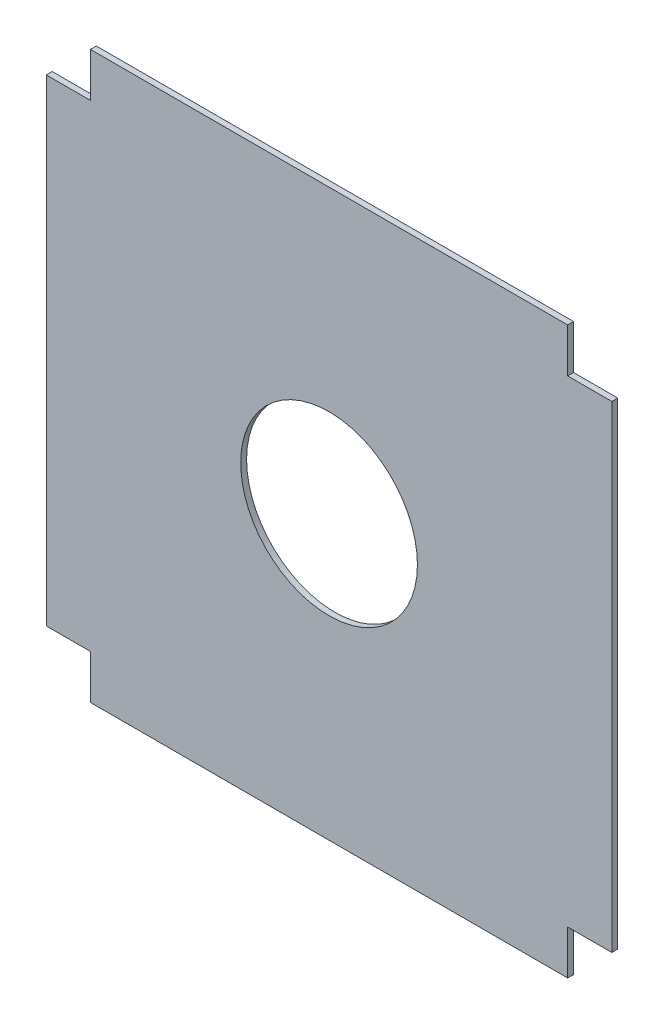
SolidWorks part; units mm, degrees
ref_plane "Front Plane" through (0, 0, 0) normal (0, 0, 1) x (1, 0, 0)
ref_plane "Top Plane" through (0, 0, 0) normal (0, 1, 0) x (1, 0, 0)
ref_plane "Right Plane" through (0, 0, 0) normal (1, 0, 0) x (0, 0, -1)
sketch "Sketch1" plane through (0, 0, 0) normal (0, 0, 1) x (1, 0, 0)
  line L0 (-48, 40.5) -> (-40.5, 40.5)
  line L1 (-40.5, 40.5) -> (-40.5, 48)
  line L2 (-40.5, 48) -> (40.5, 48)
  line L3 (40.5, 48) -> (40.5, 40.5)
  line L4 (40.5, 40.5) -> (48, 40.5)
  line L5 (48, 40.5) -> (48, -40.5)
  line L6 (48, -40.5) -> (40.5, -40.5)
  line L7 (40.5, -40.5) -> (40.5, -48)
  line L8 (40.5, -48) -> (-40.5, -48)
  line L9 (-40.5, -48) -> (-40.5, -40.5)
  line L10 (-40.5, -40.5) -> (-48, -40.5)
  line L11 (-48, -40.5) -> (-48, 40.5)
  point P0 (-40.5, 40.5)
  point P1 (-48, 40.5)
  point P2 (-40.5, 48)
  point P3 (40.5, 48)
  point P4 (40.5, 40.5)
  point P5 (48, 40.5)
  point P6 (-48, -40.5)
  point P7 (-40.5, -40.5)
  point P8 (-40.5, -48)
  point P9 (40.5, -48)
  point P10 (40.5, -40.5)
  point P11 (48, -40.5)
extrude "Boss-Extrude1" add sketch "Sketch1" along normal blind 1
sketch "Sketch2" plane through (0, 0, 1) normal (0, 0, 1) x (1, 0, 0)
  circle A0 centre (0, 0) radius 15
extrude "Cut-Extrude1" cut sketch "Sketch2" against normal blind 10
sketch "Sketch3" plane through (0, 0, 1) normal (0, 0, 1) x (1, 0, 0)
  line L0 (-13, 44) -> (-7, 44)
  line L1 (19, 44) -> (25, 44)
  line L2 (-44, 13) -> (-44, 7)
  line L3 (-44, -19) -> (-44, -25)
  line L4 (-25, -44) -> (-19, -44)
  line L5 (7, -44) -> (13, -44)
  line L6 (44, 25) -> (44, 19)
  line L7 (44, -7) -> (44, -13)
  arc A0 (25, 44) -> (-13, 44) centre (6, 44) cw
  arc A1 (19, 44) -> (-7, 44) centre (6, 44) cw
  arc A2 (-44, 13) -> (-44, -25) centre (-44, -6) cw
  arc A3 (-44, 7) -> (-44, -19) centre (-44, -6) cw
  arc A4 (-25, -44) -> (13, -44) centre (-6, -44) cw
  arc A5 (-19, -44) -> (7, -44) centre (-6, -44) cw
  arc A6 (44, -13) -> (44, 25) centre (44, 6) cw
  arc A7 (44, -7) -> (44, 19) centre (44, 6) cw
  point P2 (-13, 44)
  point P4 (-7, 44)
  point P5 (19, 44)
  point P6 (25, 44)
  point P11 (-44, 13)
  point P12 (-44, 7)
  point P13 (-44, -19)
  point P14 (-44, -25)
  point P21 (-25, -44)
  point P22 (-19, -44)
  point P23 (7, -44)
  point P24 (13, -44)
  point P31 (44, 25)
  point P32 (44, -7)
  point P33 (44, 19)
  point P34 (44, -13)
